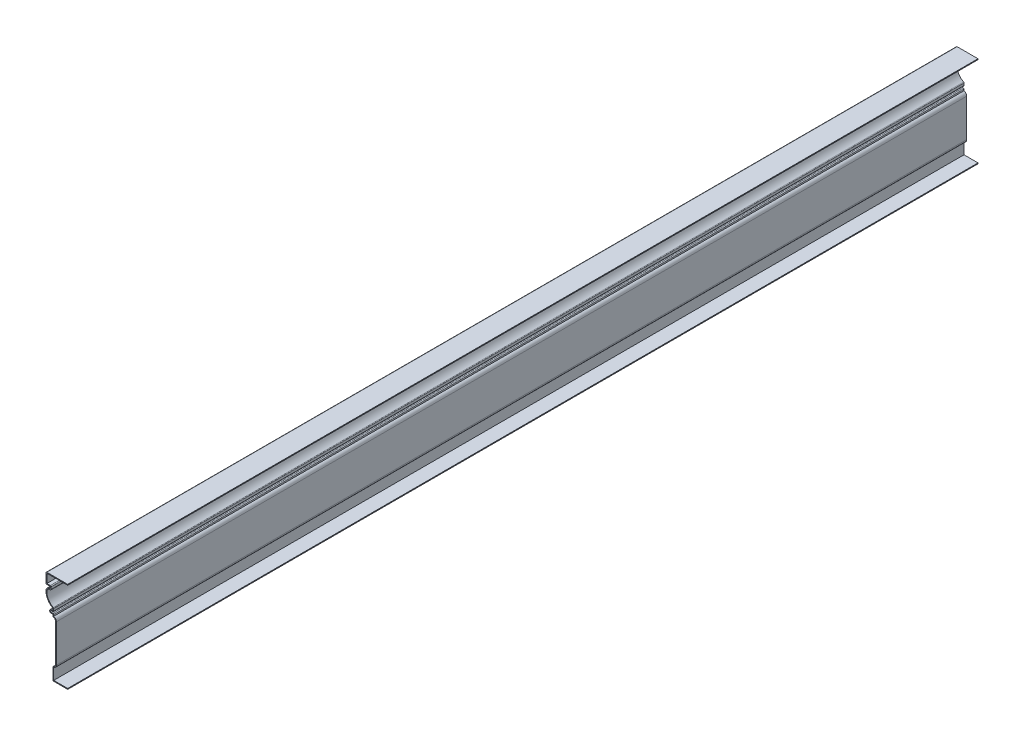
SolidWorks part; units mm, degrees
ref_plane "Front Plane" through (0, 0, 0) normal (0, 0, 1) x (1, 0, 0)
ref_plane "Top Plane" through (0, 0, 0) normal (0, 1, 0) x (1, 0, 0)
ref_plane "Right Plane" through (0, 0, 0) normal (1, 0, 0) x (0, 0, -1)
sketch "Sketch1" plane through (0, 0, 0) normal (0, 0, 1) x (1, 0, 0)
  line L0 (0, 0) -> (-22.225, 0)
  line L1 (-22.225, 0) -> (-22.225, 19.05)
  line L2 (-18.2562, 23.0187) -> (-18.2562, 79.375)
  line L3 (-22.225, 83.3438) -> (-22.225, 86.5187)
  line L4 (-22.225, 86.5187) -> (-24.765, 86.5187)
  line L5 (-24.765, 91.2812) -> (-22.225, 91.2812)
  line L6 (-22.225, 91.2812) -> (-22.225, 94.4562)
  line L7 (-26.1937, 117.475) -> (-26.1937, 120.65)
  line L8 (-32.5437, 120.65) -> (-26.1937, 120.65)
  line L9 (-32.5437, 120.65) -> (-32.5437, 136.525)
  line L10 (-32.5437, 136.525) -> (0, 136.525)
  arc A0 (-22.225, 19.05) -> (-18.2562, 23.0187) centre (-22.225, 23.0187) ccw
  arc A1 (-18.2562, 79.375) -> (-22.225, 83.3438) centre (-22.225, 79.375) ccw
  arc A2 (-24.765, 86.5187) -> (-24.765, 91.2812) centre (-24.765, 88.9) cw
  arc A3 (-22.225, 94.4562) -> (-32.4783, 112.9648) centre (-13.4937, 111.3875) cw
  arc A4 (-32.4783, 112.9648) -> (-26.1937, 117.475) centre (-27.4158, 112.5442) cw
  point P22 (-25.0673, 120.65)
  dimension "D7" = 3.9688
  dimension "D11" = 2.3812
  dimension "D16" = 5.08
  dimension "D17" = 19.05
  dimension "D1" = 136.525
  dimension "D2" = 32.5437
  dimension "D3" = 15.875
  dimension "D4" = 3.175
  dimension "D5" = 22.225
  dimension "D6" = 19.05
  dimension "D8" = 64.2938
  dimension "D9" = 3.175
  dimension "D10" = 4.7625
  dimension "D12" = 3.175
  dimension "D13" = 23.0188
  dimension "D14" = 2.54
  dimension "D15" = 6.35
extrude "Extrude-Thin1" add sketch "Sketch1" against normal blind 1365.25 thin
fillet "Fillet1" radius 1.27 10 edges at (-22.225, 0, -682.625) (-22.225, 19.05, -682.625) (-22.225, 83.3438, -682.625) (-20.955, 87.7887, -682.625) (-20.955, 90.0113, -682.625) (-20.955, 95.2488, -682.625) (-24.9237, 115.4262, -682.625) (-24.9237, 121.92, -682.625) (-32.5437, 120.65, -682.625) (-32.5437, 136.525, -682.625)
